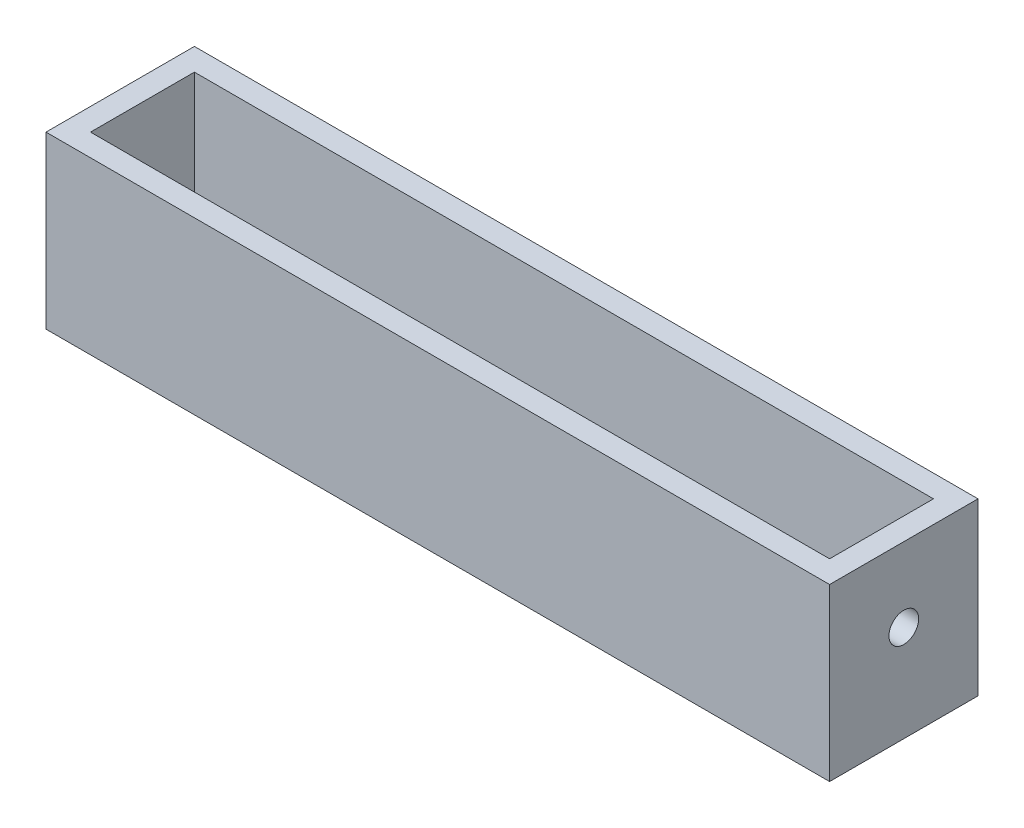
SolidWorks part; units mm, degrees
ref_plane "前视基准面" through (0, 0, 0) normal (0, 0, 1) x (1, 0, 0)
ref_plane "上视基准面" through (0, 0, 0) normal (0, 1, 0) x (1, 0, 0)
ref_plane "右视基准面" through (0, 0, 0) normal (1, 0, 0) x (0, 0, -1)
sketch "草图1" plane through (0, 0, 0) normal (0, 1, 0) x (1, 0, 0)
  line L0 (-52.8, 0) -> (-37.5, 0)
  line L1 (-52.8, -10) -> (52.8, -10)
  line L2 (-52.8, -10) -> (-52.8, 10)
  line L3 (-52.8, 10) -> (52.8, 10)
  line L4 (52.8, -10) -> (52.8, 10)
  line L5 (-52.8, -10) -> (52.8, 10) construction
  line L6 (-52.8, 10) -> (52.8, -10) construction
  line L7 (52.8, 0) -> (37.5, 0)
  circle A0 centre (-37.5, 0) radius 4
  circle A1 centre (37.5, 0) radius 4
  point P0 (0, 0)
  dimension "D1" = 105.6
  dimension "D2" = 20
extrude "凸台-拉伸1" add sketch "草图1" along normal blind 3
sketch "草图10" plane through (0, 3, 0) normal (0, 1, 0) x (1, 0, 0)
  line L1 (-52.8, -10) -> (52.8, -10)
  line L2 (-52.8, -10) -> (-52.8, 10)
  line L3 (-52.8, 10) -> (52.8, 10)
  line L4 (52.8, -10) -> (52.8, 10)
  line L5 (-52.8, -10) -> (52.8, 10) construction
  line L6 (-52.8, 10) -> (52.8, -10) construction
  line L7 (-49.8, -7) -> (49.8, -7)
  line L8 (-49.8, -7) -> (-49.8, 7)
  line L9 (-49.8, 7) -> (49.8, 7)
  line L10 (49.8, -7) -> (49.8, 7)
  line L11 (-49.8, -7) -> (49.8, 7) construction
  line L12 (-49.8, 7) -> (49.8, -7) construction
  point P0 (0, 0)
  point P7 (0, 0)
extrude "凸台-拉伸2" add sketch "草图10" along normal blind 20
sketch "草图11" plane through (-52.8, 0, 0) normal (-1, 0, 0) x (0, 0, 1)
  line L0 (0, 23) -> (0, 13)
  line L1 (-10, 23) -> (10, 23) construction
  circle A0 centre (0, 13) radius 2
extrude "切除-拉伸1" cut sketch "草图11" against normal blind 110
